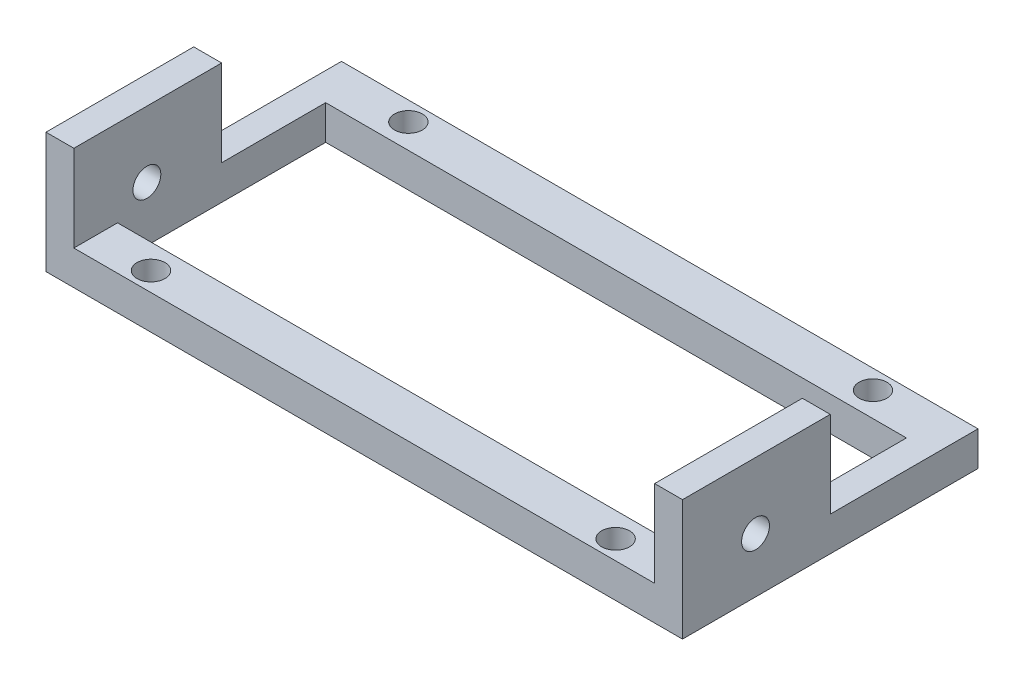
SolidWorks part; units mm, degrees
ref_plane "前视基准面" through (0, 0, 0) normal (0, 0, 1) x (1, 0, 0)
ref_plane "上视基准面" through (0, 0, 0) normal (0, 1, 0) x (1, 0, 0)
ref_plane "右视基准面" through (0, 0, 0) normal (1, 0, 0) x (0, 0, -1)
sketch "草图1" plane through (0, 0, 0) normal (0, 1, 0) x (1, 0, 0)
  line L0 (-25, 0.3) -> (25, 0.3) construction
  line L1 (-31.25, 2.35) -> (31.25, 2.35)
  line L2 (-31.25, 2.35) -> (-31.25, -2.35)
  line L3 (-31.25, -2.35) -> (31.25, -2.35)
  line L4 (31.25, 2.35) -> (31.25, -2.35)
  line L5 (-31.25, 2.35) -> (31.25, -2.35) construction
  line L6 (-31.25, -2.35) -> (31.25, 2.35) construction
  circle A0 centre (25, 0.3) radius 1.5
  circle A1 centre (-25, 0.3) radius 1.5
  point P0 (0, 0)
  point P9 (0, 0)
  point P11 (0, 0.3)
  dimension "D4" = 3
  dimension "D5" = 3
  dimension "D1" = 4.7
  dimension "D2" = 50
  dimension "D3" = 2.05
  dimension "D6" = 6.25
extrude "凸台-拉伸1" add sketch "草图1" along normal blind 3.7
sketch "草图2" plane through (-31.25, 0, 0) normal (-1, 0, 0) x (0, 0, 1)
  line L0 (-2.35, 0) -> (2.35, 0) construction
  line L1 (-2.35, 3.7) -> (29.45, 3.7)
  line L2 (-2.35, 3.7) -> (-2.35, 0)
  line L3 (-2.35, 0) -> (29.45, 0)
  line L4 (29.45, 3.7) -> (29.45, 0)
  dimension "D1" = 31.8
extrude "凸台-拉伸2" add sketch "草图2" along normal blind 3
mirror "镜向1" about plane through (0, 0, 0) normal (1, 0, 0) of "凸台-拉伸2"
ref_plane "基准面1" through (0, 0, 13.55) normal (0, 0, 1) x (1, 0, 0)
mirror "镜向2" about plane through (0, 0, 13.55) normal (0, 0, 1) of "凸台-拉伸1"
sketch "草图3" plane through (0, 0, 0) normal (0, -1, 0) x (1, 0, 0)
  line L1 (-34.25, 29.45) -> (-31.25, 29.45)
  line L2 (-34.25, 29.45) -> (-34.25, 13.55)
  line L3 (-34.25, 13.55) -> (-31.25, 13.55)
  line L4 (-31.25, 29.45) -> (-31.25, 13.55)
  line L5 (-31.25, 2.35) -> (-31.25, 24.75) construction
  line L7 (-34.25, -2.35) -> (-34.25, 29.45) construction
  point P5 (-31.25, 16.2806)
  point P6 (-34.25, 13.55)
  point P9 (-34.25, 29.7561)
  point P10 (-34.25, 29.45)
  point P13 (-34.25, 26.7508)
  point P14 (0, 0)
extrude "凸台-拉伸3" add sketch "草图3" against normal blind 13
sketch "草图4" plane through (-34.25, 0, 0) normal (-1, 0, 0) x (0, 0, 1)
  line L0 (-2.35, 0) -> (29.45, 0) construction
  circle A0 centre (21.5927, 5.9) radius 1.5
  point P4 (21.5927, 5.9)
  point P5 (0, 0)
  point P6 (5.9085, 5.9)
  dimension "D2" = 3
  dimension "D1" = 5.9
extrude "切除-拉伸1" cut sketch "草图4" against normal blind 13
mirror "镜向3" about plane through (0, 0, 0) normal (1, 0, 0) of "切除-拉伸1", "凸台-拉伸3"
